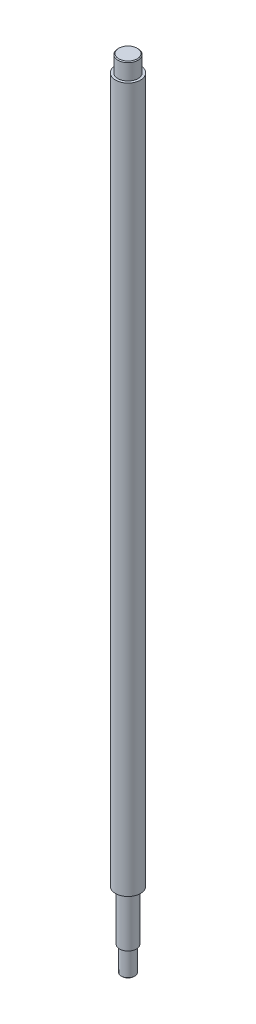
SolidWorks part; units mm, degrees
ref_plane "Front Plane" through (0, 0, 0) normal (0, 0, 1) x (1, 0, 0)
ref_plane "Top Plane" through (0, 0, 0) normal (0, 1, 0) x (1, 0, 0)
ref_plane "Right Plane" through (0, 0, 0) normal (1, 0, 0) x (0, 0, -1)
ref_plane "Plane1" through (0, 0, 0) normal (0, 0, 1) x (1, 0, 0)
sketch "Sketch4" plane through (0, 0, 0) normal (0, 1, 0) x (1, 0, 0)
  circle A0 centre (0, 0) radius 7.5
  dimension "D1" = 15
extrude "Boss-Extrude1" add sketch "Sketch4" along normal blind 421
sketch "Sketch5" plane through (0, 421, 0) normal (0, 1, 0) x (1, 0, 0)
  circle A0 centre (0, 0) radius 6
  dimension "D1" = 12
extrude "Boss-Extrude2" add sketch "Sketch5" along normal blind 10
chamfer "Chamfer1" distance 0.5 angle 45 1 edges at (0, 431, 6)
sketch "Sketch6" plane through (0, 0, 0) normal (0, -1, 0) x (1, 0, 0)
  circle A0 centre (0, 0) radius 5
  dimension "D1" = 10
extrude "Boss-Extrude3" add sketch "Sketch6" along normal blind 30
sketch "Sketch7" plane through (0, -30, 0) normal (0, -1, 0) x (1, 0, 0)
  circle A0 centre (0, 0) radius 4
  dimension "D1" = 8
extrude "Boss-Extrude4" add sketch "Sketch7" along normal blind 15
chamfer "Chamfer2" distance 0.5 angle 45 1 edges at (0, -45, -4)
